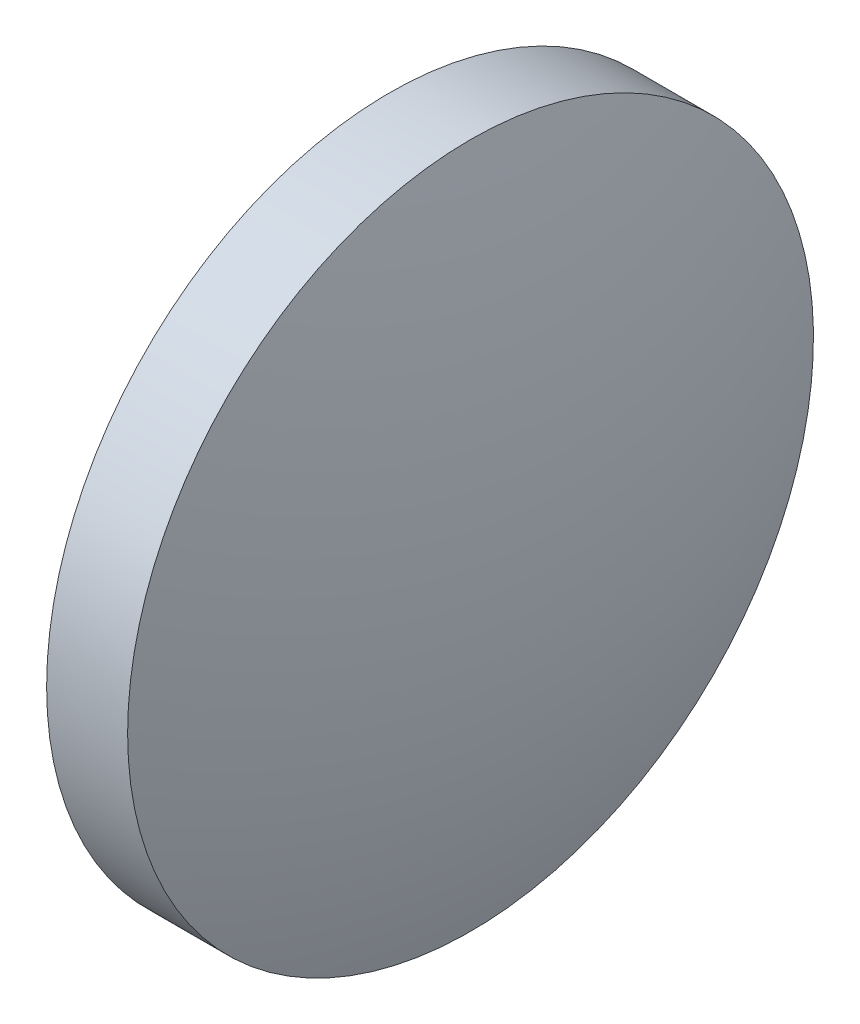
SolidWorks part; units mm, degrees
ref_plane "前视基准面" through (0, 0, 0) normal (0, 0, 1) x (1, 0, 0)
ref_plane "上视基准面" through (0, 0, 0) normal (0, 1, 0) x (1, 0, 0)
ref_plane "右视基准面" through (0, 0, 0) normal (1, 0, 0) x (0, 0, -1)
sketch "草图1" plane through (0, 0, 0) normal (0, 0, 1) x (1, 0, 0)
  line L0 (604.3781, 118.7374) -> (611.8965, 118.7374) construction
  line L1 (606.6386, 118.7374) -> (606.6386, 125.0874)
  line L2 (606.6386, 125.0874) -> (608.1386, 125.0874)
  line L3 (609.1386, 118.7374) -> (606.6386, 118.7374)
  arc A0 (609.1386, 118.7374) -> (608.1386, 125.0874) centre (588.4774, 118.7374) ccw
revolve "旋转1" add sketch "草图1" angle 360 about L0
